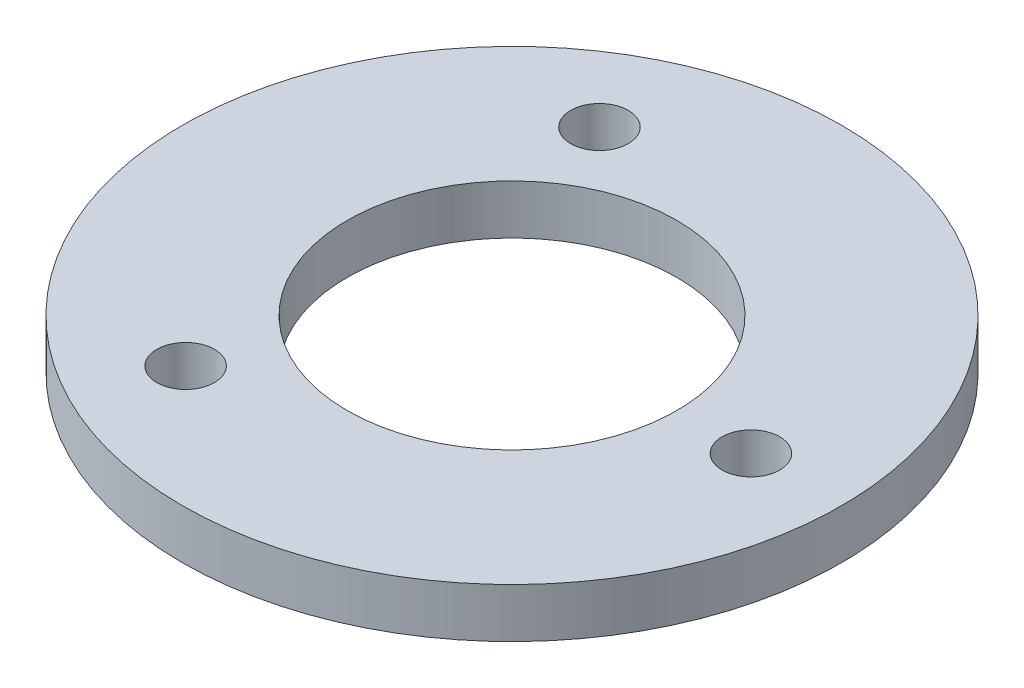
SolidWorks part; units mm, degrees
ref_plane "Front Plane" through (0, 0, 0) normal (0, 0, 1) x (1, 0, 0)
ref_plane "Top Plane" through (0, 0, 0) normal (0, 1, 0) x (1, 0, 0)
ref_plane "Right Plane" through (0, 0, 0) normal (1, 0, 0) x (0, 0, -1)
sketch "Sketch1" plane through (0, 0, 0) normal (0, 1, 0) x (1, 0, 0)
  circle A0 centre (0, 0) radius 10
  circle A1 centre (0, 0) radius 20
  circle A2 centre (14.5, 0) radius 1.75
  circle A3 centre (-7.25, -12.5574) radius 1.75
  circle A4 centre (-7.25, 12.5574) radius 1.75
  point P13 (0, 0)
  dimension "D1" = 40
  dimension "D2" = 20
  dimension "D3" = 3.5
  dimension "D4" = 14.5
  dimension "D5" = 3
extrude "Boss-Extrude1" add sketch "Sketch1" along normal blind 3
